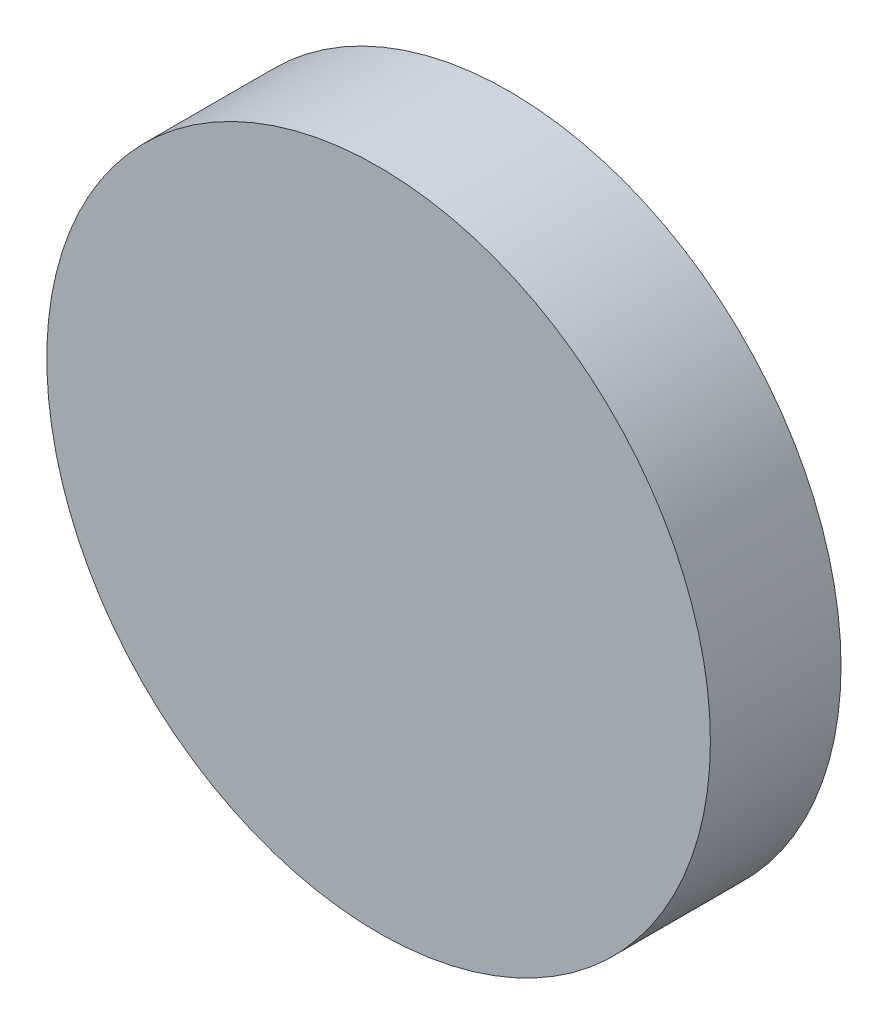
SolidWorks part; units mm, degrees
ref_plane "前视基准面" through (0, 0, 0) normal (0, 0, 1) x (1, 0, 0)
ref_plane "上视基准面" through (0, 0, 0) normal (0, 1, 0) x (1, 0, 0)
ref_plane "右视基准面" through (0, 0, 0) normal (1, 0, 0) x (0, 0, -1)
sketch "草图1" plane through (0, 0, 0) normal (0, 0, 1) x (1, 0, 0)
  circle A0 centre (0, 0) radius 25.4
  dimension "D1" = 50.8
extrude "凸台-拉伸1" add sketch "草图1" along normal blind 10 contours A0
